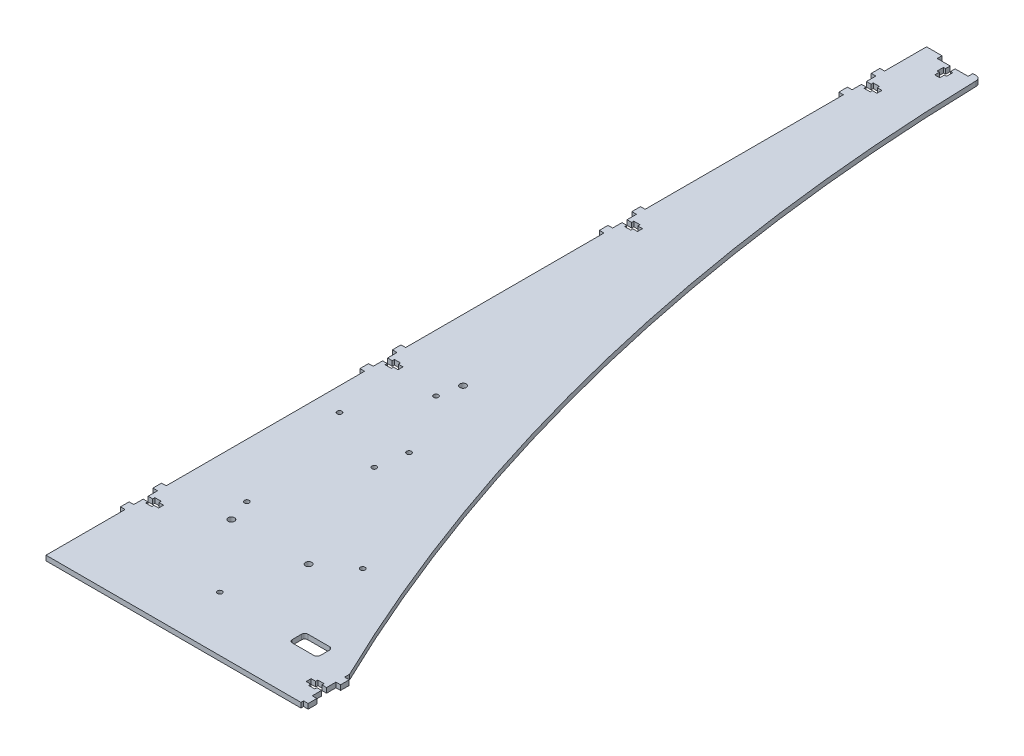
SolidWorks part; units mm, degrees
ref_plane "Alzado" through (0, 0, 0) normal (0, 0, 1) x (1, 0, 0)
ref_plane "Planta" through (0, 0, 0) normal (0, 1, 0) x (1, 0, 0)
ref_plane "Vista lateral" through (0, 0, 0) normal (1, 0, 0) x (0, 0, -1)
sketch "Croquis1" plane through (0, 0, 0) normal (0, 1, 0) x (1, 0, 0)
  line L0 (7, 66.1) -> (10, 66.1)
  line L1 (0, 0) -> (165, 0)
  line L2 (0, 0) -> (0, 51)
  line L3 (0, 570) -> (10, 570)
  line L4 (165, 0) -> (165, 1.5)
  line L5 (0, 51) -> (-3, 51)
  line L7 (0, 57) -> (-3, 57)
  line L8 (-3, 51) -> (-3, 57)
  line L9 (0, 72) -> (-3, 72)
  line L11 (0, 78) -> (-3, 78)
  line L12 (-3, 72) -> (-3, 78)
  line L13 (0, 66.1) -> (3, 66.1)
  line L15 (0, 62.9) -> (3, 62.9)
  line L16 (10, 66.1) -> (10, 62.9)
  line L17 (7, 67.5) -> (3, 67.5)
  line L18 (7, 67.5) -> (7, 66.1)
  line L19 (7, 61.5) -> (3, 61.5)
  line L20 (3, 67.5) -> (3, 66.1)
  line L21 (3, 62.9) -> (3, 61.5)
  line L22 (7, 62.9) -> (7, 61.5)
  line L23 (7, 62.9) -> (10, 62.9)
  line L24 (0, 66.1) -> (0, 72)
  line L25 (0, 78) -> (0, 206)
  line L26 (0, 57) -> (0, 62.9)
  line L27 (0, 233) -> (-3, 233)
  line L28 (-3, 227) -> (-3, 233)
  line L29 (0, 227) -> (-3, 227)
  line L30 (0, 221.1) -> (3, 221.1)
  line L31 (3, 222.5) -> (3, 221.1)
  line L32 (7, 222.5) -> (3, 222.5)
  line L33 (7, 222.5) -> (7, 221.1)
  line L34 (7, 221.1) -> (10, 221.1)
  line L35 (10, 221.1) -> (10, 217.9)
  line L36 (7, 217.9) -> (10, 217.9)
  line L37 (7, 217.9) -> (7, 216.5)
  line L38 (7, 216.5) -> (3, 216.5)
  line L39 (3, 217.9) -> (3, 216.5)
  line L40 (0, 217.9) -> (3, 217.9)
  line L41 (0, 212) -> (-3, 212)
  line L42 (-3, 206) -> (-3, 212)
  line L43 (0, 206) -> (-3, 206)
  line L44 (0, 388) -> (-3, 388)
  line L45 (-3, 382) -> (-3, 388)
  line L46 (0, 382) -> (-3, 382)
  line L47 (0, 376.1) -> (3, 376.1)
  line L48 (3, 377.5) -> (3, 376.1)
  line L49 (7, 377.5) -> (3, 377.5)
  line L50 (7, 377.5) -> (7, 376.1)
  line L51 (7, 376.1) -> (10, 376.1)
  line L52 (10, 376.1) -> (10, 372.9)
  line L53 (7, 372.9) -> (10, 372.9)
  line L54 (7, 372.9) -> (7, 371.5)
  line L55 (7, 371.5) -> (3, 371.5)
  line L56 (3, 372.9) -> (3, 371.5)
  line L57 (0, 372.9) -> (3, 372.9)
  line L58 (0, 367) -> (-3, 367)
  line L59 (-3, 361) -> (-3, 367)
  line L60 (0, 361) -> (-3, 361)
  line L61 (0, 388) -> (0, 516)
  line L62 (0, 376.1) -> (0, 382)
  line L63 (0, 367) -> (0, 372.9)
  line L64 (0, 233) -> (0, 361)
  line L65 (0, 221.1) -> (0, 227)
  line L66 (0, 212) -> (0, 217.9)
  line L67 (21.6, 566.9) -> (30, 566.9)
  line L69 (10, 570) -> (10, 566.9)
  line L70 (10, 566.9) -> (18.4, 566.9)
  line L71 (30, 570) -> (30, 566.9)
  line L73 (18.4, 566.9) -> (18.4, 563.9)
  line L74 (18.4, 556.9) -> (21.6, 556.9)
  line L75 (21.6, 566.9) -> (21.6, 563.9)
  line L76 (17, 563.9) -> (18.4, 563.9)
  line L77 (17, 563.9) -> (17, 559.9)
  line L78 (17, 559.9) -> (18.4, 559.9)
  line L79 (23, 563.9) -> (23, 559.9)
  line L80 (21.6, 563.9) -> (23, 563.9)
  line L81 (18.4, 559.9) -> (18.4, 556.9)
  line L82 (21.6, 559.9) -> (21.6, 556.9)
  line L83 (21.6, 559.9) -> (23, 559.9)
  line L84 (30, 570) -> (165, 570)
  line L85 (158, 13.4) -> (158, 12)
  line L86 (165, 1.5) -> (168, 1.5)
  line L88 (165, 7.5) -> (168, 7.5)
  line L89 (168, 1.5) -> (168, 7.5)
  line L90 (165, 22.5) -> (168, 22.5)
  line L92 (165, 28.5) -> (168, 28.5)
  line L93 (168, 22.5) -> (168, 28.5)
  line L94 (165, 16.6) -> (162, 16.6)
  line L96 (165, 13.4) -> (162, 13.4)
  line L97 (155, 16.6) -> (155, 13.4)
  line L98 (158, 18) -> (162, 18)
  line L99 (158, 18) -> (158, 16.6)
  line L100 (158, 12) -> (162, 12)
  line L101 (162, 18) -> (162, 16.6)
  line L102 (158, 16.6) -> (155, 16.6)
  line L103 (162, 13.4) -> (162, 12)
  line L104 (158, 13.4) -> (155, 13.4)
  line L105 (165, 16.6) -> (165, 22.5)
  line L106 (165, 7.5) -> (165, 13.4)
  line L107 (165, 28.5) -> (165, 570)
  line L108 (0, 543) -> (-3, 543)
  line L109 (-3, 537) -> (-3, 543)
  line L110 (0, 537) -> (-3, 537)
  line L111 (0, 531.1) -> (3, 531.1)
  line L112 (3, 532.5) -> (3, 531.1)
  line L113 (7, 532.5) -> (3, 532.5)
  line L114 (7, 532.5) -> (7, 531.1)
  line L115 (7, 531.1) -> (10, 531.1)
  line L116 (10, 531.1) -> (10, 527.9)
  line L117 (7, 527.9) -> (10, 527.9)
  line L118 (7, 527.9) -> (7, 526.5)
  line L119 (7, 526.5) -> (3, 526.5)
  line L120 (3, 527.9) -> (3, 526.5)
  line L121 (0, 527.9) -> (3, 527.9)
  line L122 (0, 522) -> (-3, 522)
  line L123 (-3, 516) -> (-3, 522)
  line L124 (0, 516) -> (-3, 516)
  line L125 (0, 543) -> (0, 570)
  line L126 (0, 522) -> (0, 527.9)
  line L127 (0, 531.1) -> (0, 537)
  dimension "D1" = 570
  dimension "D2" = 165
  dimension "D3" = 3
  dimension "D4" = 6
  dimension "D5" = 3
  dimension "D6" = 6
  dimension "D7" = 15
  dimension "D8" = 10
  dimension "D9" = 3.2
  dimension "D10" = 5.9
  dimension "D11" = 4
  dimension "D12" = 6
  dimension "D13" = 1.4
  dimension "D14" = 51
  dimension "D15" = 3
  dimension "D17" = 155
  dimension "D18" = 20
  dimension "D19" = 10
  dimension "D20" = 3.1
  dimension "D21" = 10
  dimension "D22" = 3.2
  dimension "D23" = 4
  dimension "D24" = 6
  dimension "D25" = 1.4
  dimension "D26" = 8.4
  dimension "D27" = 3
  dimension "D28" = 6
  dimension "D29" = 6
  dimension "D30" = 3
  dimension "D31" = 3
  dimension "D32" = 3.2
  dimension "D33" = 4
  dimension "D34" = 6
  dimension "D35" = 1.4
  dimension "D36" = 10
  dimension "D37" = 3
  dimension "D38" = 15
  dimension "D39" = 5.9
  dimension "D40" = 1.5
  dimension "D16" = 4
extrude "Saliente-Extruir1" add sketch "Croquis1" along normal blind 3.2
sketch "Croquis3" plane through (0, 3.2, 0) normal (0, 1, 0) x (1, 0, 0)
  line L0 (0, 217.9) -> (0, 212) construction
  line L1 (0, 0) -> (165, 0) construction
  circle A0 centre (40, 80) radius 2.05
  circle A1 centre (90, 80) radius 2.05
  circle A2 centre (40, 230) radius 2.05
  dimension "D1" = 4.1
  dimension "D2" = 50
  dimension "D3" = 150
  dimension "D4" = 40
  dimension "D5" = 80
extrude "Cortar-Extruir2" cut sketch "Croquis3" against normal up to surface (3.2 mm away) up to face at (34.1167, 0, -285.1383)
sketch "Croquis4" plane through (0, 0, 0) normal (0, -1, 0) x (1, 0, 0)
  line L1 (0, 0) -> (165, 0) construction
  line L4 (143, -30.5) -> (129, -30.5)
  line L5 (145, -32.5) -> (145, -38.5)
  line L6 (143, -40.5) -> (129, -40.5)
  line L7 (127, -32.5) -> (127, -38.5)
  line L8 (165, -28.5) -> (165, -570) construction
  arc A14 (143, -30.5) -> (145, -32.5) centre (143, -32.5) cw
  arc A15 (127, -38.5) -> (129, -40.5) centre (129, -38.5) ccw
  arc A16 (127, -32.5) -> (129, -30.5) centre (129, -32.5) cw
  arc A17 (145, -38.5) -> (143, -40.5) centre (143, -38.5) cw
  point P38 (145, -30.5)
  point P41 (127, -40.5)
  point P46 (145, -40.5)
  dimension "D3" = 20
  dimension "D20" = 2
  dimension "D16" = 18
  dimension "D17" = 10
  dimension "D19" = 30.5
extrude "Cortar-Extruir3" cut sketch "Croquis4" against normal up to surface (3.2 mm away) up to face at (40, 3.2, -227.95)
sketch "Croquis5" plane through (0, 0, 0) normal (0, -1, 0) x (1, 0, 0)
  line L0 (165, -570) -> (30, -570) construction
  line L1 (165, -28.5) -> (165, -570) construction
  line L2 (35, -570) -> (165, -570)
  line L3 (165, -570) -> (165, -31.5)
  arc A0 (35, -570) -> (165, -31.5) centre (1334.6806, -598.8159) cw
  dimension "D3" = 1300
  dimension "D1" = 5
  dimension "D2" = 3
extrude "Cortar-Extruir4" cut sketch "Croquis5" against normal up to surface (3.2 mm away) up to face at (136, 3.2, -35.5)
fillet "Redondeo1" radius 3 1 edges at (35, 1.6, -570)
sketch "Croquis6" plane through (0, 0, 0) normal (0, -1, 0) x (1, 0, 0)
  line L0 (0, -51) -> (0, 0) construction
  line L1 (0, 0) -> (165, 0) construction
  line L2 (0, -206) -> (0, -78) construction
  line L3 (127, -35.5) -> (77, -35.5) construction
  line L4 (127, -32.5) -> (127, -38.5) construction
  circle A0 centre (110, -95) radius 1.55
  circle A1 centre (35, -95) radius 1.55
  circle A2 centre (60, -175) radius 1.55
  circle A4 centre (15, -175) radius 1.55
  circle A5 centre (77, -35.5) radius 1.55
  circle A6 centre (37, -215.5) radius 1.55
  circle A7 centre (57, -155.5) radius 1.55
  dimension "D1" = 3.1
  dimension "D2" = 75
  dimension "D3" = 35
  dimension "D4" = 95
  dimension "D5" = 45
  dimension "D6" = 15
  dimension "D7" = 80
  dimension "D8" = 50
  dimension "D9" = 180
  dimension "D10" = 40
  dimension "D11" = 120
  dimension "D12" = 20
extrude "Cortar-Extruir5" cut sketch "Croquis6" against normal up to surface (3.2 mm away) up to face at (33.8773, 3.2, -285.3182)
sketch "Croquis7" plane through (0, 0, 0) normal (0, -1, 0) x (1, 0, 0)
  line L0 (165, -28.5) -> (165, -31.5) construction
  line L1 (-3, -543) -> (0, -543)
  line L2 (-3, -543) -> (-3, -542.8)
  line L3 (-3, -542.8) -> (0, -542.8)
  line L4 (0, -543) -> (0, -542.8)
  line L5 (-3, -537) -> (0, -537)
  line L6 (-3, -537) -> (-3, -537.2)
  line L7 (-3, -537.2) -> (0, -537.2)
  line L8 (0, -537) -> (0, -537.2)
  line L9 (-3, -522) -> (0, -522)
  line L10 (-3, -522) -> (-3, -521.8)
  line L11 (-3, -521.8) -> (0, -521.8)
  line L12 (0, -522) -> (0, -521.8)
  line L13 (-3, -516) -> (0, -516)
  line L14 (-3, -516) -> (-3, -516.2)
  line L15 (-3, -516.2) -> (0, -516.2)
  line L16 (0, -516) -> (0, -516.2)
  line L17 (-3, -388) -> (0, -388)
  line L18 (-3, -388) -> (-3, -387.8)
  line L19 (-3, -387.8) -> (0, -387.8)
  line L20 (0, -388) -> (0, -387.8)
  line L21 (-3, -382) -> (0, -382)
  line L22 (-3, -382) -> (-3, -382.2)
  line L23 (-3, -382.2) -> (0, -382.2)
  line L24 (0, -382) -> (0, -382.2)
  line L25 (-3, -367) -> (0, -367)
  line L26 (-3, -367) -> (-3, -366.8)
  line L27 (-3, -366.8) -> (0, -366.8)
  line L28 (0, -367) -> (0, -366.8)
  line L29 (-3, -361) -> (0, -361)
  line L30 (-3, -361) -> (-3, -361.2)
  line L31 (-3, -361.2) -> (0, -361.2)
  line L32 (0, -361) -> (0, -361.2)
  line L33 (-3, -233) -> (0, -233)
  line L34 (-3, -233) -> (-3, -232.8)
  line L35 (-3, -232.8) -> (0, -232.8)
  line L36 (0, -233) -> (0, -232.8)
  line L37 (-3, -227) -> (0, -227)
  line L38 (-3, -227) -> (-3, -227.2)
  line L39 (-3, -227.2) -> (0, -227.2)
  line L40 (0, -227) -> (0, -227.2)
  line L41 (-3, -212) -> (0, -212)
  line L42 (-3, -212) -> (-3, -211.8)
  line L43 (-3, -211.8) -> (0, -211.8)
  line L44 (0, -212) -> (0, -211.8)
  line L45 (-3, -206) -> (0, -206)
  line L46 (-3, -206) -> (-3, -206.2)
  line L47 (-3, -206.2) -> (0, -206.2)
  line L48 (0, -206) -> (0, -206.2)
  line L49 (-3, -78) -> (0, -78)
  line L50 (-3, -78) -> (-3, -77.8)
  line L51 (-3, -77.8) -> (0, -77.8)
  line L52 (0, -78) -> (0, -77.8)
  line L53 (-3, -72) -> (0, -72)
  line L54 (-3, -72) -> (-3, -72.2)
  line L55 (-3, -72.2) -> (0, -72.2)
  line L56 (0, -72) -> (0, -72.2)
  line L57 (-3, -51) -> (0, -51)
  line L58 (-3, -57) -> (0, -57)
  line L59 (-3, -57) -> (-3, -56.8)
  line L60 (-3, -56.8) -> (0, -56.8)
  line L61 (0, -57) -> (0, -56.8)
  line L62 (-3, -51) -> (-3, -51.2)
  line L63 (-3, -51.2) -> (0, -51.2)
  line L64 (0, -51) -> (0, -51.2)
  line L65 (168, -28.5) -> (165, -28.5)
  line L66 (168, -28.5) -> (168, -28.3)
  line L67 (168, -28.3) -> (165, -28.3)
  line L68 (165, -28.5) -> (165, -28.3)
  line L70 (168, -22.5) -> (165, -22.5)
  line L71 (168, -22.5) -> (168, -22.7)
  line L72 (168, -22.7) -> (165, -22.7)
  line L73 (165, -22.5) -> (165, -22.7)
  line L74 (168, -7.5) -> (165, -7.5)
  line L75 (168, -7.5) -> (168, -7.3)
  line L76 (168, -7.3) -> (165, -7.3)
  line L77 (165, -7.5) -> (165, -7.3)
  line L78 (168, -1.5) -> (165, -1.5)
  line L79 (168, -1.5) -> (168, -1.7)
  line L80 (168, -1.7) -> (165, -1.7)
  line L81 (165, -1.5) -> (165, -1.7)
  dimension "D1" = 0.2
  dimension "D2" = 0.2
  dimension "D3" = 0.2
  dimension "D4" = 0.2
  dimension "D5" = 0.2
  dimension "D6" = 0.2
  dimension "D7" = 0.2
  dimension "D8" = 0.2
  dimension "D9" = 0.2
  dimension "D10" = 0.2
  dimension "D11" = 0.2
  dimension "D12" = 0.2
  dimension "D13" = 0.2
  dimension "D14" = 0.2
  dimension "D15" = 0.2
  dimension "D16" = 0.2
  dimension "D17" = 0.2
  dimension "D18" = 0.2
  dimension "D19" = 0.2
  dimension "D20" = 0.2
extrude "Cortar-Extruir6" cut sketch "Croquis7" against normal up to surface (3.2 mm away) up to face at (110, 3.2, -93.45)
